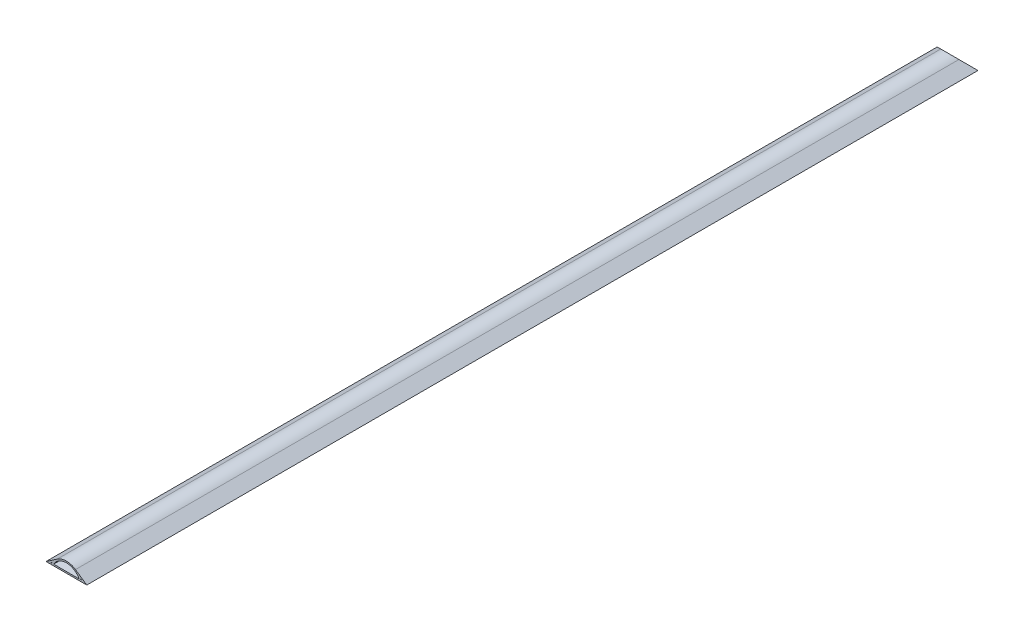
SolidWorks part; units mm, degrees
material "PUR"
ref_plane "Front Plane" through (0, 0, 0) normal (0, 0, 1) x (1, 0, 0)
ref_plane "Top Plane" through (0, 0, 0) normal (0, 1, 0) x (1, 0, 0)
ref_plane "Right Plane" through (0, 0, 0) normal (1, 0, 0) x (0, 0, -1)
sketch "Sketch2" plane through (0, 0, 0) normal (0, 0, 1) x (1, 0, 0)
  line L0 (0, 0) -> (68.58, 0)
  line L1 (34.29, 0) -> (34.29, 17.78) construction
  line L2 (18.9927, 13.0354) -> (0, 0)
  line L3 (49.5873, 13.0354) -> (68.58, 0)
  line L4 (10.9978, 4.4675) -> (8.1894, 2.54)
  line L5 (8.1894, 2.54) -> (9.965, 2.54)
  line L6 (57.5822, 4.4675) -> (60.3906, 2.54)
  line L7 (20.43, 10.9412) -> (8.1894, 2.54) construction
  line L8 (48.15, 10.9412) -> (60.3906, 2.54) construction
  line L9 (12.8231, 2.54) -> (55.7569, 2.54)
  line L10 (8.1894, 2.54) -> (60.3906, 2.54) construction
  line L11 (58.615, 2.54) -> (60.3906, 2.54)
  arc A0 (58.615, 2.54) -> (57.5822, 4.4675) centre (34.29, -9.2529) ccw
  arc A1 (55.7569, 2.54) -> (12.8231, 2.54) centre (34.29, -9.2529) ccw
  circle A2 centre (34.29, -9.2529) radius 27.0329 construction
  circle A3 centre (34.29, -9.2529) radius 24.4929 construction
  arc A4 (10.9978, 4.4675) -> (9.965, 2.54) centre (34.29, -9.2529) ccw
  arc A5 (49.5873, 13.0354) -> (18.9927, 13.0354) centre (34.29, -9.2529) ccw
  point P7 (59.69, 0)
  dimension "D1" = 68.58
  dimension "D2" = 17.78
  dimension "D3" = 8.89
  dimension "D4" = 2.54
  dimension "D5" = 2.54
extrude "Boss-Extrude1" add sketch "Sketch2" along normal blind 1498.6
sketch "Sketch3" plane through (0, 0, 0) normal (1, 0, 0) x (0, 0, -1)
  line L0 (-17.78, 17.78) -> (0, 0)
  line L1 (0, 0) -> (0, 17.78)
  line L2 (0, 17.78) -> (-17.78, 17.78)
  line L3 (0, 13.0354) -> (0, 0) construction
  line L4 (0, 13.0354) -> (0, 17.78) construction
  line L5 (0, 13.0354) -> (0, 0) construction
  line L6 (0, 13.0354) -> (0, 17.78) construction
  dimension "D1" = 45
extrude "Cut-Extrude1" cut sketch "Sketch3" along normal through all
